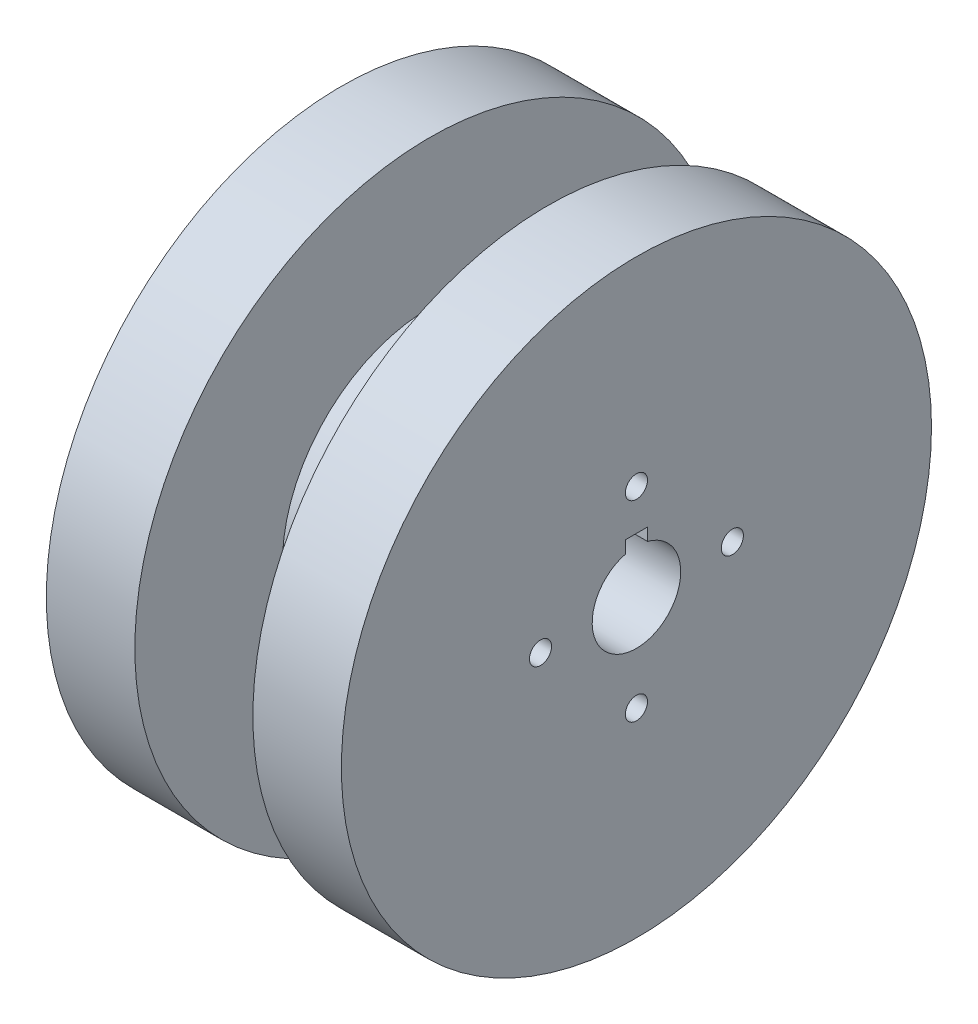
SolidWorks part; units mm, degrees
material "6061-T6 (SS)"
ref_plane "Plano frontal" through (0, 0, 0) normal (0, 0, 1) x (1, 0, 0)
ref_plane "Plano superior" through (0, 0, 0) normal (0, 1, 0) x (1, 0, 0)
ref_plane "Plano direito" through (0, 0, 0) normal (1, 0, 0) x (0, 0, -1)
sketch "Esboço5" plane through (0, 0, 0) normal (0, 0, 1) x (1, 0, 0)
  line L0 (0, 0) -> (0, 40)
  line L1 (0, 40) -> (12, 40)
  line L2 (12, 40) -> (12, 20)
  line L4 (28, 20) -> (28, 40)
  line L5 (28, 40) -> (40, 40)
  line L6 (40, 40) -> (40, 0)
  line L7 (40, 0) -> (0, 0)
  line L9 (12, 20) -> (28, 20)
  point P9 (0, 0)
  dimension "D1" = 40
revolve "Revolução1" add sketch "Esboço5" angle 360 about L7
sketch "Esboço6" plane through (0, 0, 0) normal (-1, 0, 0) x (0, 0, 1)
  line L0 (-1.5, 7.5) -> (-1.5, 5.8095)
  line L1 (0, 7.5) -> (1.5, 7.5)
  line L5 (-1.5, 7.5) -> (0, 7.5)
  line L6 (1.5, 7.5) -> (1.5, 5.8095)
  circle A0 centre (0, 0) radius 6
extrude "Corte-extrusão3" cut sketch "Esboço6" against normal through all contours A0 | A0 L6 L1 L5 L0
sketch "Esboço7" plane through (0, 0, 0) normal (-1, 0, 0) x (0, 0, 1)
  circle A1 centre (0, 13.0017) radius 1.5
  circle A2 centre (13.0017, 0) radius 1.5
  circle A3 centre (0, -13.0017) radius 1.5
  circle A4 centre (-13.0017, 0) radius 1.5
extrude "Corte-extrusão4" cut sketch "Esboço7" against normal through all
sketch "Esboço9" plane through (0, 0, 0) normal (-1, 0, 0) x (0, 0, 1)
  line L1 (0, -32.8452) -> (32.8452, 0)
  line L2 (32.8452, 0) -> (0, 32.8452)
  line L3 (0, 32.8452) -> (-32.8452, 0)
  line L4 (-32.8452, 0) -> (0, -32.8452)
  circle A0 centre (0, 0) radius 23.225 construction
extrude "Corte-extrusão6" cut sketch "Esboço9" against normal blind 4
sketch "Esboço10" plane through (0, 0, 0) normal (-1, 0, 0) x (0, 0, 1)
  line L1 (25.1235, 25.1235) -> (-25.1235, 25.1235)
  line L2 (-25.1235, 25.1235) -> (-25.1235, -25.1235)
  line L3 (-25.1235, -25.1235) -> (25.1235, -25.1235)
  line L4 (25.1235, -25.1235) -> (25.1235, 25.1235)
  circle A0 centre (0, 0) radius 25.1235 construction
extrude "Corte-extrusão7" cut sketch "Esboço10" against normal blind 3
